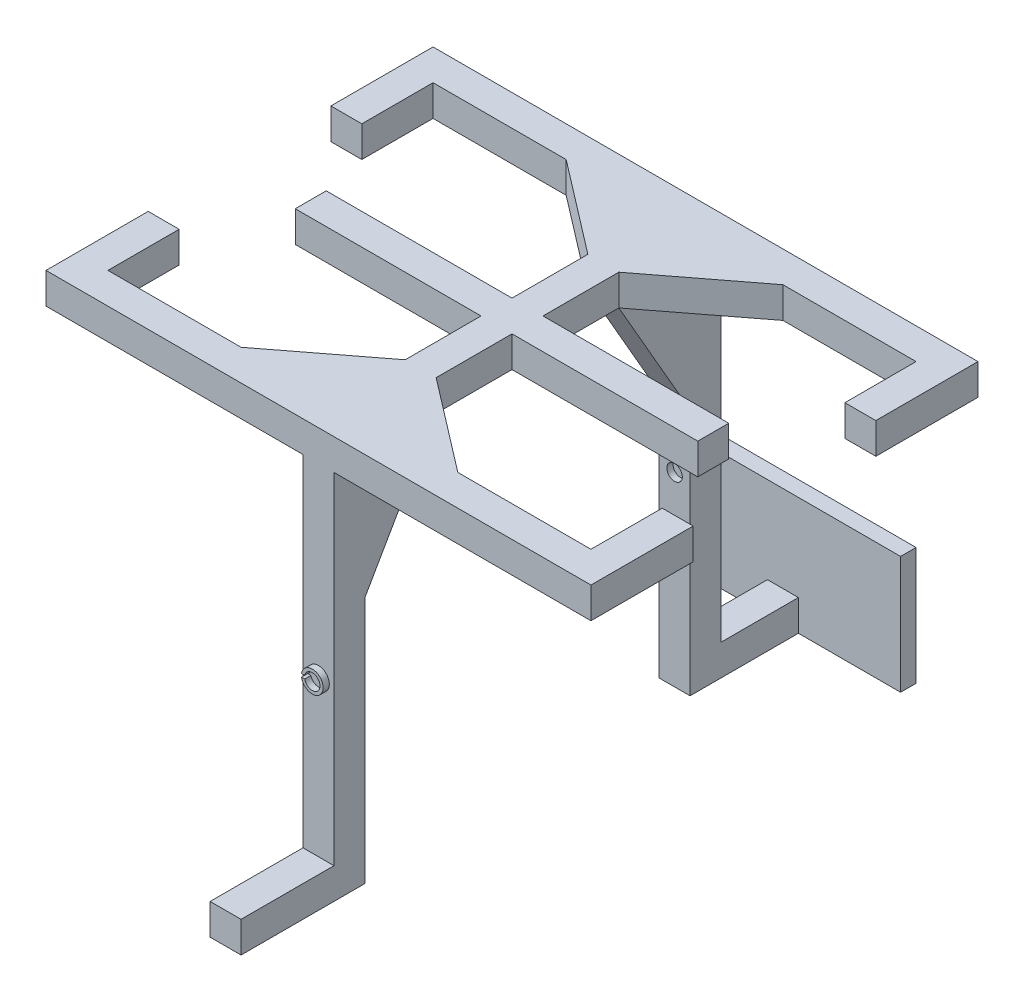
SolidWorks part; units mm, degrees
ref_plane "Front Plane" through (0, 0, 0) normal (0, 0, 1) x (1, 0, 0)
ref_plane "Top Plane" through (0, 0, 0) normal (0, 1, 0) x (1, 0, 0)
ref_plane "Right Plane" through (0, 0, 0) normal (1, 0, 0) x (0, 0, -1)
sketch "Sketch1" plane through (0, 0, 0) normal (0, 0, 1) x (1, 0, 0)
  line L1 (0, 0) -> (176, 0)
  line L2 (0, 0) -> (0, 10)
  line L3 (0, 10) -> (176, 10)
  line L4 (176, 0) -> (176, 10)
  dimension "D1" = 176
  dimension "D2" = 10
extrude "Boss-Extrude1" add sketch "Sketch1" along normal blind 10
sketch "Sketch2" plane through (0, 0, 0) normal (0, 0, -1) x (-1, 0, 0)
  line L0 (-88, 0) -> (-88, 10) construction
  line L2 (0, 0) -> (-176, 0) construction
  line L3 (-176, 10) -> (0, 10) construction
  line L9 (-83, 10) -> (-93, 10)
  line L10 (-83, 10) -> (-83, 0)
  line L11 (-83, 0) -> (-93, 0)
  line L12 (-93, 10) -> (-93, 0)
  line L13 (-83, 10) -> (-93, 0) construction
  line L14 (-83, 0) -> (-93, 10) construction
  point P6 (-88, 5)
  dimension "D1" = 10
extrude "Boss-Extrude2" add sketch "Sketch2" along normal blind 52.5
sketch "Sketch3" plane through (0, 0, 0) normal (0, 0, -1) x (-1, 0, 0)
  line L0 (-83, 10) -> (0, 10) construction
  line L1 (0, 0) -> (-10, 0)
  line L2 (0, 0) -> (0, 10)
  line L3 (0, 10) -> (-10, 10)
  line L4 (-10, 0) -> (-10, 10)
  line L5 (-83, 0) -> (-93, 0) construction
  line L6 (-176, 10) -> (-93, 10) construction
  line L7 (-176, 0) -> (-166, 0)
  line L8 (-176, 0) -> (-176, 10)
  line L9 (-176, 10) -> (-166, 10)
  line L10 (-166, 0) -> (-166, 10)
  dimension "D1" = 10
extrude "Boss-Extrude3" add sketch "Sketch3" along normal blind 23
mirror "Mirror6" about plane through (0, 0, -52.5) normal (0, 0, 1) of bodies 108 109
sketch "Sketch4" plane through (0, 0, 0) normal (0, -1, 0) x (1, 0, 0)
  line L0 (0, 10) -> (176, 10) construction
  line L1 (93, 0) -> (83, 0)
  line L2 (93, 0) -> (93, 10)
  line L3 (93, 10) -> (83, 10)
  line L4 (83, 0) -> (83, 10)
  line L5 (83, -52.5) -> (93, -52.5) construction
  line L6 (83, -105) -> (83, 0) construction
  line L7 (93, -105) -> (93, 0) construction
  line L8 (93, -105) -> (93, -115)
  line L9 (93, -115) -> (83, -115)
  line L10 (83, -105) -> (83, -115)
  line L11 (93, -105) -> (83, -105)
  dimension "D1" = 10
extrude "Boss-Extrude4" add sketch "Sketch4" along normal blind 120
sketch "Sketch13" plane through (83, 0, 0) normal (-1, 0, 0) x (0, 0, 1)
  line L0 (-105, 0) -> (-82, 0)
  line L1 (-105, 0) -> (0, 0) construction
  line L2 (-105, 0) -> (-105, -40)
  line L3 (-105, -120) -> (-105, 0) construction
  line L4 (-105, -40) -> (-82, 0)
  line L5 (0, -40) -> (0, 0)
  line L6 (0, -120) -> (0, 0) construction
  line L7 (0, 0) -> (-23, 0)
  line L8 (-23, 0) -> (0, -40)
extrude "Boss-Extrude5" add sketch "Sketch13" against normal blind 10
sketch "Sketch15" plane through (83, 0, 0) normal (-1, 0, 0) x (0, 0, 1)
  line L0 (-52.5, 10) -> (-52.5, 0) construction
  line L1 (-105, 10) -> (0, 10) construction
  line L2 (-82, 0) -> (-23, 0) construction
sketch "Sketch17" plane through (83, 0, 0) normal (-1, 0, 0) x (0, 0, 1)
  line L0 (-52.5, 0) -> (-52.5, 10) construction
  line L1 (-82, 0) -> (-23, 0) construction
  line L3 (-47.5, 10) -> (-57.5, 10)
  line L4 (-47.5, 10) -> (-47.5, 0)
  line L5 (-47.5, 0) -> (-57.5, 0)
  line L6 (-57.5, 10) -> (-57.5, 0)
  line L7 (-47.5, 10) -> (-57.5, 0) construction
  line L8 (-47.5, 0) -> (-57.5, 10) construction
  point P5 (-52.5, 5)
  dimension "D1" = 10
extrude "Boss-Extrude6" add sketch "Sketch17" along normal blind 20
sketch "Sketch18" plane through (0, 0, 0) normal (0, -1, 0) x (1, 0, 0)
  line L5 (71, -52.5) -> (65, -52.5)
  arc A1 (65, -52.5) -> (71, -52.5) centre (68, -52.5) ccw
revolve "Cut-Revolve2" cut sketch "Sketch18" angle 180 about L5
pattern_linear "LPattern1" count 3 spacing 20 along (-1, 0, 0) of "Boss-Extrude6", "Cut-Revolve2"
sketch "Sketch20" plane through (0, 0, 0) normal (0, -1, 0) x (1, 0, 0)
  line L0 (88, -23) -> (88, -82) construction
  line L1 (93, -23) -> (83, -23) construction
  line L2 (93, -82) -> (83, -82) construction
  line L3 (88, -52.5) -> (5.9948, -15.4171) construction
  line L4 (2.9948, -15.4171) -> (8.9948, -15.4171)
  arc A0 (2.9948, -15.4171) -> (8.9948, -15.4171) centre (5.9948, -15.4171) cw
  point P11 (5.9948, -15.4171)
sketch "Sketch23" plane through (93, 0, 0) normal (1, 0, 0) x (0, 0, -1)
  line L0 (52.5, 0) -> (52.5, 10) construction
  line L1 (82, 0) -> (23, 0) construction
  line L2 (105, 10) -> (0, 10) construction
  line L4 (57.5, 10) -> (47.5, 10)
  line L5 (57.5, 10) -> (57.5, 0)
  line L6 (57.5, 0) -> (47.5, 0)
  line L7 (47.5, 10) -> (47.5, 0)
  line L8 (57.5, 10) -> (47.5, 0) construction
  line L9 (57.5, 0) -> (47.5, 10) construction
  point P6 (52.5, 5)
  dimension "D1" = 10
extrude "Boss-Extrude7" add sketch "Sketch23" along normal blind 20
sketch "Sketch24" plane through (0, 0, 0) normal (0, -1, 0) x (1, 0, 0)
  line L5 (111, -52.5) -> (105, -52.5)
  arc A1 (105, -52.5) -> (111, -52.5) centre (108, -52.5) cw
revolve "Cut-Revolve3" cut sketch "Sketch24" angle 180 about L5
pattern_linear "LPattern2" count 3 spacing 20 along (1, 0, 0) of "Boss-Extrude7", "Cut-Revolve3"
sketch "Sketch25" plane through (0, 0, -115) normal (0, 0, -1) x (-1, 0, 0)
  line L0 (-83, -120) -> (-83, 0) construction
  line L1 (-93, -120) -> (-83, -120)
  line L2 (-93, -120) -> (-93, -110)
  line L3 (-93, -110) -> (-83, -110)
  line L4 (-83, -120) -> (-83, -110)
  dimension "D1" = 10
extrude "Boss-Extrude8" add sketch "Sketch25" along normal blind 30
sketch "Sketch27" plane through (0, 0, 10) normal (0, 0, 1) x (1, 0, 0)
  line L0 (83, -120) -> (83, 0) construction
  line L1 (93, -120) -> (83, -120)
  line L2 (93, -120) -> (93, -110)
  line L3 (93, -110) -> (83, -110)
  line L4 (83, -120) -> (83, -110)
  dimension "D1" = 10
extrude "Boss-Extrude10" add sketch "Sketch27" along normal blind 30
sketch "Sketch28" plane through (0, 0, -145) normal (0, 0, -1) x (-1, 0, 0)
  line L0 (-88, -120) -> (-88, -101) construction
  line L1 (-93, -120) -> (-83, -120) construction
  line L3 (-50, -82) -> (-126, -82)
  line L4 (-50, -82) -> (-50, -120)
  line L5 (-50, -120) -> (-126, -120)
  line L6 (-126, -82) -> (-126, -120)
  line L7 (-50, -82) -> (-126, -120) construction
  line L8 (-50, -120) -> (-126, -82) construction
  dimension "D1" = 76
extrude "Boss-Extrude11" add sketch "Sketch28" against normal blind 5
sketch "Sketch30" plane through (0, 0, 0) normal (0, -1, 0) x (1, 0, 0)
  line L0 (93, -105) -> (123, -105)
  line L1 (93, -105) -> (166, -105) construction
  line L2 (93, -105) -> (93, -82)
  line L3 (93, -82) -> (123, -105)
  line L4 (93, 0) -> (93, -23)
  line L5 (93, 0) -> (123, 0)
  line L6 (93, 0) -> (166, 0) construction
  line L7 (123, 0) -> (93, -23)
extrude "Boss-Extrude12" add sketch "Sketch30" against normal blind 10
pattern_circular "CirPattern2" count 2 every 180 about axis through (88, 0, -52.5) along (0, 1, 0) of "Boss-Extrude12"
sketch "Sketch31" plane through (0, 0, -115) normal (0, 0, -1) x (-1, 0, 0)
  line L0 (-88, -110) -> (-88, -60) construction
  line L1 (-83, -110) -> (-93, -110) construction
  circle A0 centre (-88, -60) radius 2.5
  circle A1 centre (-88, -60) radius 3.5
extrude "Boss-Extrude13" add sketch "Sketch31" along normal blind 2
sketch "Sketch32" plane through (0, 0, 10) normal (0, 0, 1) x (1, 0, 0)
  line L0 (88, -110) -> (88, -60) construction
  line L1 (93, -110) -> (83, -110) construction
  circle A0 centre (88, -60) radius 2.5
  circle A1 centre (88, -60) radius 3.5
extrude "Boss-Extrude14" add sketch "Sketch32" along normal blind 2
sketch "Sketch33" plane through (0, 0, -105) normal (0, 0, 1) x (1, 0, 0)
  line L0 (88, -120) -> (88, -60) construction
  line L1 (93, -120) -> (83, -120) construction
  circle A0 centre (88, -60) radius 2.5
extrude "Cut-Extrude1" cut sketch "Sketch33" against normal blind 2
sketch "Sketch34" plane through (0, 0, 0) normal (0, 0, -1) x (-1, 0, 0)
  line L0 (-88, -120) -> (-88, -60) construction
  line L1 (-83, -120) -> (-93, -120) construction
  circle A0 centre (-88, -60) radius 2.5
extrude "Cut-Extrude2" cut sketch "Sketch34" against normal blind 2
sketch "Sketch35" plane through (0, 0, 12) normal (0, 0, 1) x (1, 0, 0)
  line L1 (86.6943, -60.5) -> (84.3057, -60.5)
  line L2 (86.6943, -60.5) -> (86.6943, -59.5)
  line L3 (86.6943, -59.5) -> (84.3057, -59.5)
  line L4 (84.3057, -60.5) -> (84.3057, -59.5)
  line L5 (86.6943, -60.5) -> (84.3057, -59.5) construction
  line L6 (86.6943, -59.5) -> (84.3057, -60.5) construction
  circle A0 centre (88, -60) radius 2.5 construction
  point P0 (85.5, -60)
  dimension "D1" = 1
extrude "Cut-Extrude3" cut sketch "Sketch35" against normal blind 2
sketch "Sketch37" plane through (0, 0, -117) normal (0, 0, -1) x (-1, 0, 0)
  line L0 (-90.5, -60) -> (-91.5, -60) construction
  line L2 (-89.86, -59.5) -> (-92.14, -59.5)
  line L3 (-89.86, -59.5) -> (-89.86, -60.5)
  line L4 (-89.86, -60.5) -> (-92.14, -60.5)
  line L5 (-92.14, -59.5) -> (-92.14, -60.5)
  line L6 (-89.86, -59.5) -> (-92.14, -60.5) construction
  line L7 (-89.86, -60.5) -> (-92.14, -59.5) construction
  circle A0 centre (-88, -60) radius 2.5 construction
  circle A1 centre (-88, -60) radius 3.5 construction
  point P7 (-91, -60)
  dimension "D1" = 1
extrude "Cut-Extrude4" cut sketch "Sketch37" against normal blind 2
sketch "Sketch40" plane through (0, 0, 0) normal (0, -1, 0) x (1, 0, 0)
  line L0 (108, -52.5) -> (88, -52.5) construction
  line L1 (88, -52.5) -> (103.5584, -100.0177) construction
  line L2 (103.5584, -100.0177) -> (106.5584, -100.0177)
  line L3 (103.5584, -100.0177) -> (100.5584, -100.0177)
  arc A1 (100.5584, -100.0177) -> (106.5584, -100.0177) centre (103.5584, -100.0177) cw
  dimension "D1" = 50
revolve "Cut-Revolve4" cut sketch "Sketch40" angle 180 about L2
revolve "Cut-Revolve5" cut sketch "Sketch20" angle 180 about L4
sketch "Sketch42" plane through (0, -120, 0) normal (0, -1, 0) x (1, 0, 0)
  line L0 (88, 38) -> (88, 32)
  arc A0 (88, 38) -> (88, 32) centre (88, 35) ccw
revolve "Cut-Revolve8" cut sketch "Sketch42" angle 180 about L0
sketch "Sketch43" plane through (0, 0, 0) normal (0, -1, 0) x (1, 0, 0)
  line L0 (83, -47.5) -> (93, -57.5) construction
  line L2 (83, -57.5) -> (93, -47.5) construction
sketch "Sketch44" plane through (0, -120, 0) normal (0, -1, 0) x (1, 0, 0)
  line L0 (88, -107) -> (88, -113)
  arc A1 (88, -107) -> (88, -113) centre (88, -110) ccw
revolve "Cut-Revolve9" cut sketch "Sketch44" angle 180 about L0
